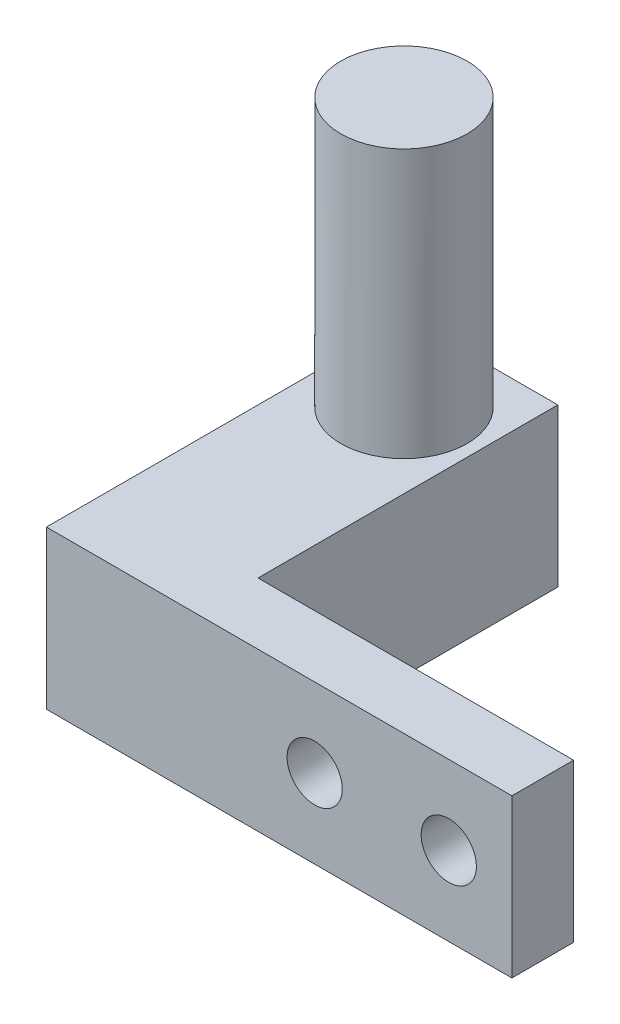
SolidWorks part; units mm, degrees
ref_plane "Front Plane" through (0, 0, 0) normal (0, 0, 1) x (1, 0, 0)
ref_plane "Top Plane" through (0, 0, 0) normal (0, 1, 0) x (1, 0, 0)
ref_plane "Right Plane" through (0, 0, 0) normal (1, 0, 0) x (0, 0, -1)
sketch "Sketch1" plane through (0, 0, 0) normal (0, 0, 1) x (1, 0, 0)
  line L1 (0, 0) -> (12.5, 0)
  line L2 (0, 0) -> (0, 10)
  line L3 (0, 10) -> (12.5, 10)
  line L4 (12.5, 0) -> (12.5, 10)
  dimension "D1" = 12.5
  dimension "D2" = 10
extrude "Boss-Extrude1" add sketch "Sketch1" along normal blind 10
sketch "Sketch2" plane through (0, 0, 0) normal (-1, 0, 0) x (0, 0, 1)
  line L0 (10, 0) -> (0, 0) construction
  line L1 (10, 0) -> (0, 0)
  line L2 (10, 0) -> (10, 10)
  line L3 (10, 10) -> (0, 10)
  line L4 (0, 0) -> (0, 10)
  line L5 (0, 10) -> (0, 0) construction
extrude "Boss-Extrude2" add sketch "Sketch2" along normal blind 5
sketch "Sketch3" plane through (0, 10, 0) normal (0, 1, 0) x (1, 0, 0)
  line L0 (12.5, -10) -> (12.5, 0) construction
  line L1 (12.5, 0) -> (-5, 0) construction
  circle A0 centre (3.75, -5) radius 4
  point P5 (12.5, -5)
  point P9 (3.75, 0)
  dimension "D1" = 8
extrude "Boss-Extrude3" add sketch "Sketch3" along normal blind 17
sketch "Sketch4" plane through (0, 10, 0) normal (0, 1, 0) x (1, 0, 0)
  line L0 (12.5, 0) -> (-5, 0) construction
  line L1 (12.5, 0) -> (8.5, 0)
  line L2 (12.5, 0) -> (12.5, -10)
  line L3 (12.5, -10) -> (8.5, -10)
  line L4 (8.5, 0) -> (8.5, -10)
  line L5 (12.5, -10) -> (-5, -10) construction
  line L6 (12.5, -10) -> (12.5, 0) construction
  line L7 (3.75, 0) -> (3.75, -3.716) construction
  line L8 (-5, -10) -> (-1, -10)
  line L9 (-5, 0) -> (-5, -10)
  line L10 (-5, 0) -> (-1, 0)
  line L11 (-1, 0) -> (-1, -10)
  dimension "D1" = 4
extrude "Cut-Extrude1" cut sketch "Sketch4" against normal through all
sketch "Sketch5" plane through (0, 0, 10) normal (0, 0, 1) x (1, 0, 0)
  line L0 (-1, 0) -> (8.5, 0) construction
  line L1 (8.5, 0) -> (-1, 0)
  line L2 (8.5, 0) -> (8.5, 10)
  line L3 (8.5, 10) -> (-1, 10)
  line L4 (-1, 0) -> (-1, 10)
  line L5 (-1, 0) -> (-1, 10) construction
  line L6 (8.5, 10) -> (-1, 10) construction
  line L7 (8.5, 0) -> (8.5, 10) construction
extrude "Boss-Extrude4" add sketch "Sketch5" along normal blind 12.5
sketch "Sketch6" plane through (8.5, 0, 0) normal (1, 0, 0) x (0, 0, -1)
  line L0 (0, 10) -> (-22.5, 10) construction
  line L1 (-22.5, 0) -> (-17.5, 0)
  line L2 (-22.5, 0) -> (-22.5, 10)
  line L3 (-22.5, 10) -> (-17.5, 10)
  line L4 (-17.5, 0) -> (-17.5, 10)
  line L5 (-22.5, 0) -> (-22.5, 10) construction
  line L6 (0, 0) -> (-22.5, 0) construction
  dimension "D1" = 5
extrude "Boss-Extrude5" add sketch "Sketch6" along normal blind 30
sketch "Sketch7" plane through (0, 0, 22.5) normal (0, 0, 1) x (1, 0, 0)
  line L0 (38.5, 10) -> (38.5, 0) construction
  circle A0 centre (22.5, 5) radius 1.75
  circle A1 centre (33.5, 5) radius 1.75
  point P6 (38.5, 5)
  dimension "D1" = 3.5
  dimension "D2" = 3.5
  dimension "D3" = 5
  dimension "D4" = 11
extrude "Cut-Extrude2" cut sketch "Sketch7" against normal through all
sketch "Sketch8" plane through (0, 10, 0) normal (0, 1, 0) x (1, 0, 0)
  line L0 (38.5, -22.5) -> (-1, -22.5) construction
  line L1 (38.5, -17.5) -> (8.5, -17.5)
  line L2 (38.5, -17.5) -> (38.5, -22.5)
  line L3 (38.5, -22.5) -> (8.5, -22.5)
  line L4 (8.5, -17.5) -> (8.5, -22.5)
  line L5 (8.5, 0) -> (8.5, -17.5) construction
extrude "Cut-Extrude4" cut sketch "Sketch8" against normal blind 10
sketch "Sketch10" plane through (0, 0, 22.5) normal (0, 0, 1) x (1, 0, 0)
  line L0 (8.5, 0) -> (8.5, 10) construction
  line L1 (8.5, 10) -> (-1, 10)
  line L2 (8.5, 10) -> (8.5, 0)
  line L3 (8.5, 0) -> (-1, 0)
  line L4 (-1, 10) -> (-1, 0)
  line L5 (-1, 0) -> (8.5, 0) construction
  line L6 (-1, 10) -> (-1, 0) construction
  line L7 (8.5, 10) -> (-1, 10) construction
extrude "Cut-Extrude6" cut sketch "Sketch10" against normal blind 3.49
sketch "Sketch11" plane through (0, 0, 19.01) normal (0, 0, 1) x (1, 0, 0)
  line L0 (8.5, 0) -> (8.5, 10) construction
  line L1 (8.5, 10) -> (-1, 10)
  line L2 (8.5, 10) -> (8.5, 0)
  line L3 (8.5, 0) -> (-1, 0)
  line L4 (-1, 10) -> (-1, 0)
  line L5 (-1, 10) -> (-1, 0) construction
  line L6 (8.5, 10) -> (-1, 10) construction
  line L7 (-1, 0) -> (8.5, 0) construction
extrude "Boss-Extrude6" add sketch "Sketch11" along normal blind 3.9
sketch "Sketch12" plane through (8.5, 0, 0) normal (1, 0, 0) x (0, 0, -1)
  line L0 (-22.91, 0) -> (-22.91, 10) construction
  line L1 (-22.91, 10) -> (-18.91, 10)
  line L2 (-22.91, 10) -> (-22.91, 0)
  line L3 (-22.91, 0) -> (-18.91, 0)
  line L4 (-18.91, 10) -> (-18.91, 0)
  line L5 (0, 10) -> (-22.91, 10) construction
  line L6 (0, 0) -> (-22.91, 0) construction
  dimension "D1" = 4
extrude "Boss-Extrude7" add sketch "Sketch12" along normal blind 20
sketch "Sketch13" plane through (0, 0, 0) normal (0, -1, 0) x (-1, 0, 0)
  line L0 (-28.5, -18.91) -> (-8.5, -18.91) construction
  line L1 (-8.5, -18.91) -> (-28.5, -18.91)
  line L2 (-8.5, -18.91) -> (-8.5, -19)
  line L3 (-8.5, -19) -> (-28.5, -19)
  line L4 (-28.5, -18.91) -> (-28.5, -19)
  line L5 (-28.5, -22.91) -> (-28.5, -18.91) construction
  line L6 (-8.5, 0) -> (-8.5, -18.91) construction
  dimension "D1" = 0.09
extrude "Cut-Extrude7" cut sketch "Sketch13" against normal through all
sketch "Sketch14" plane through (0, 0, 22.91) normal (0, 0, 1) x (1, 0, 0)
  line L0 (-1, 10) -> (-1, 0) construction
  line L1 (-1, 0) -> (28.5, 0) construction
  line L2 (28.5, 10) -> (28.5, 0) construction
  circle A0 centre (16, 5) radius 1.75
  circle A1 centre (24.5, 5) radius 1.75
  dimension "D1" = 3.5
  dimension "D4" = 3.5
  dimension "D2" = 17
  dimension "D3" = 5
  dimension "D5" = 4
extrude "Cut-Extrude8" cut sketch "Sketch14" against normal through all
